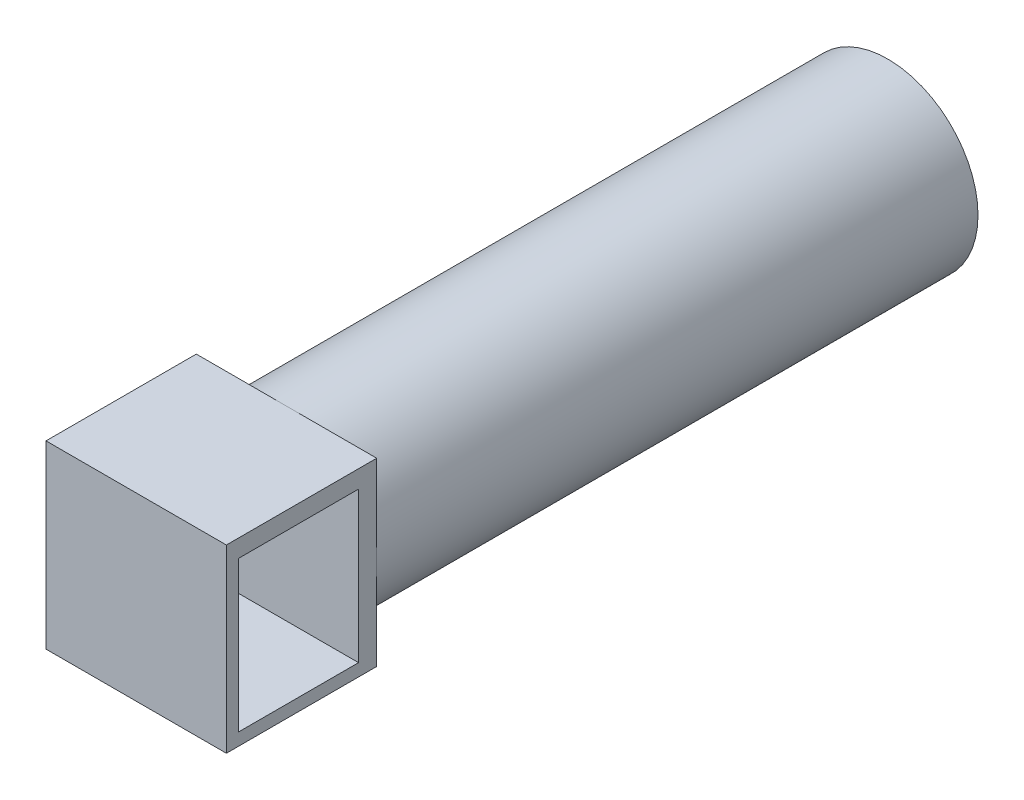
SolidWorks part; units mm, degrees
ref_plane "Płaszczyzna przednia" through (0, 0, 0) normal (0, 0, 1) x (1, 0, 0)
ref_plane "Płaszczyzna górna" through (0, 0, 0) normal (0, 1, 0) x (1, 0, 0)
ref_plane "Płaszczyzna prawa" through (0, 0, 0) normal (1, 0, 0) x (0, 0, -1)
sketch "Szkic1" plane through (0, 0, 0) normal (0, 0, 1) x (1, 0, 0)
  circle A0 centre (0, 0) radius 30
extrude "Dodanie-wyciągnięcie1" add sketch "Szkic1" along normal blind 200
sketch "Szkic2" plane through (0, 0, 0) normal (1, 0, 0) x (0, 0, -1)
  line L1 (-200, 30) -> (-250, 30)
  line L2 (-200, 30) -> (-200, -30)
  line L3 (-200, -30) -> (-250, -30)
  line L4 (-250, 30) -> (-250, -30)
  dimension "D1" = 50
  dimension "D2" = 60
extrude "Dodanie-wyciągnięcie2" add sketch "Szkic2" along normal mid plane 60
sketch "Szkic3" plane through (30, 0, 0) normal (1, 0, 0) x (0, 0, -1)
  line L1 (-206.0379, 24.1261) -> (-246.0379, 24.1261)
  line L2 (-206.0379, 24.1261) -> (-206.0379, -25.8739)
  line L3 (-206.0379, -25.8739) -> (-246.0379, -25.8739)
  line L4 (-246.0379, 24.1261) -> (-246.0379, -25.8739)
  line L5 (-206.0379, 24.1261) -> (-246.0379, -25.8739) construction
  line L6 (-206.0379, -25.8739) -> (-246.0379, 24.1261) construction
  point P0 (-226.0379, -0.8739)
  dimension "D1" = 40
  dimension "D2" = 50
extrude "Wytnij-wyciągnięcie1" cut sketch "Szkic3" against normal through all
